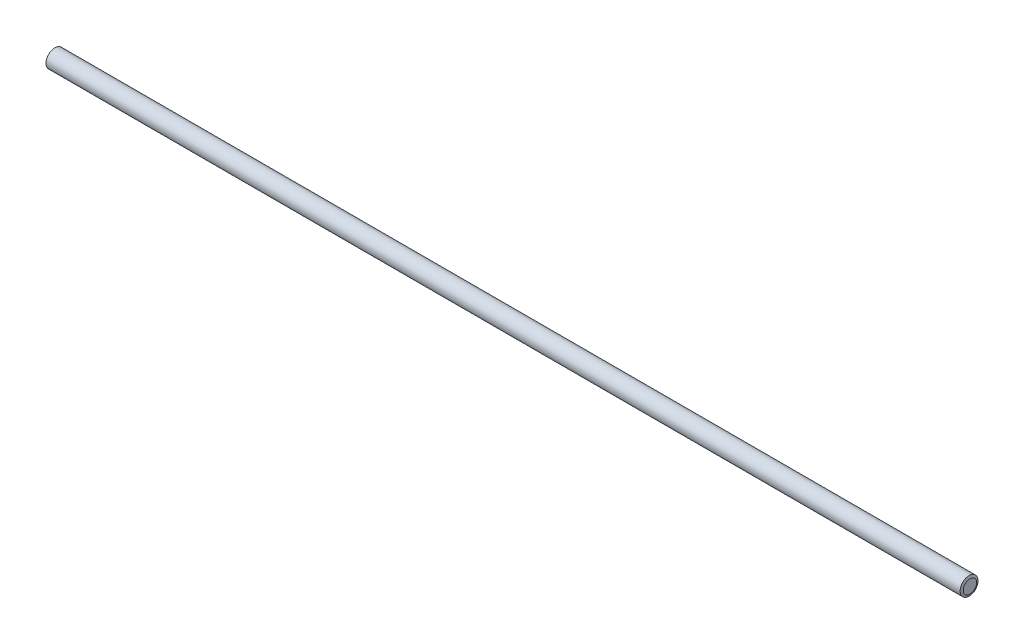
SolidWorks part; units mm, degrees
material "Alloy Steel"
ref_plane "Front Plane" through (0, 0, 0) normal (0, 0, 1) x (1, 0, 0)
ref_plane "Top Plane" through (0, 0, 0) normal (0, 1, 0) x (1, 0, 0)
ref_plane "Right Plane" through (0, 0, 0) normal (1, 0, 0) x (0, 0, -1)
ref_plane "Plane1" through (0, 0, 0) normal (0, 0, 1) x (1, 0, 0)
sketch "Sketch1" plane through (0, 0, 0) normal (0, 0, 1) x (1, 0, 0)
  line L0 (0, 0) -> (0, 3.7369)
  line L1 (0, 3.7369) -> (0.5, 5)
  line L2 (0.5, 5) -> (511.5, 5)
  line L3 (511.5, 5) -> (512, 3.7369)
  line L4 (512, 3.7369) -> (512, 0)
  line L5 (512, 0) -> (0, 0)
  line L6 (512, 0) -> (0, 0) construction
  line L7 (256, 0) -> (256, 5) construction
  dimension "D1" = 512
  dimension "D2" = 21.597
  dimension "D3" = 5
  dimension "D4" = 1.2631
  dimension "D5" = 21.597
revolve "Revolve1" add sketch "Sketch1" angle 360 about L6
ref_plane "Plane2" through (256, 0, 0) normal (-1, 0, 0) x (0, 0, 1)
